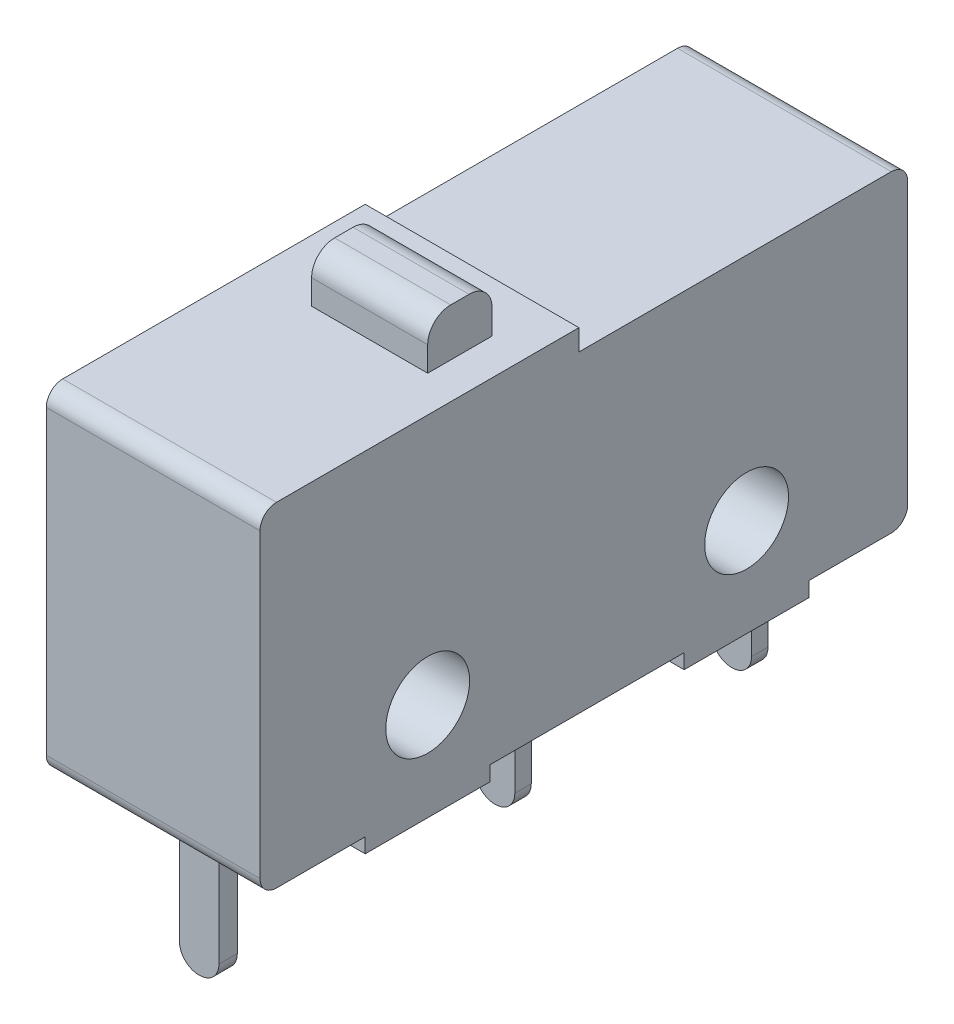
SolidWorks part; units mm, degrees
ref_plane "Front Plane" through (0, 0, 0) normal (0, 0, 1) x (1, 0, 0)
ref_plane "Top Plane" through (0, 0, 0) normal (0, 1, 0) x (1, 0, 0)
ref_plane "Right Plane" through (0, 0, 0) normal (1, 0, 0) x (0, 0, -1)
sketch "Sketch1" plane through (0, 0, 0) normal (1, 0, 0) x (0, 0, -1)
  line L0 (-37.3731, 0) -> (-34.6731, 0)
  line L1 (-37.8731, 0.5) -> (-37.8731, 9.66)
  line L2 (-37.3731, 10.16) -> (-28.1731, 10.16)
  line L3 (-28.1731, 10.16) -> (-28.1731, 9.52)
  line L4 (-28.1731, 9.52) -> (-18.6731, 9.52)
  line L5 (-18.1731, 9.02) -> (-18.1731, 0.5)
  line L6 (-34.6731, 0) -> (-34.6731, -0.45)
  line L7 (-34.6731, -0.45) -> (-30.8731, -0.45)
  line L8 (-30.8731, -0.45) -> (-30.8731, 0)
  line L9 (-30.8731, 0) -> (-24.9731, 0)
  line L10 (-24.9731, 0) -> (-24.9731, -0.45)
  line L11 (-24.9731, -0.45) -> (-21.1731, -0.45)
  line L12 (-21.1731, -0.45) -> (-21.1731, 0)
  line L13 (-21.1731, 0) -> (-18.6731, 0)
  line L14 (-32.7731, -0.45) -> (-32.7731, 2.9938) construction
  line L15 (-23.0731, -0.45) -> (-23.0731, 2.9938) construction
  arc A0 (-18.6731, 9.52) -> (-18.1731, 9.02) centre (-18.6731, 9.02) cw
  arc A1 (-18.6731, 0) -> (-18.1731, 0.5) centre (-18.6731, 0.5) ccw
  arc A2 (-37.3731, 0) -> (-37.8731, 0.5) centre (-37.3731, 0.5) cw
  arc A3 (-37.8731, 9.66) -> (-37.3731, 10.16) centre (-37.3731, 9.66) cw
  circle A4 centre (-32.7731, 2.525) radius 1.275
  circle A5 centre (-23.0731, 2.525) radius 1.275
  point P18 (-23.0731, -0.45)
  point P19 (-18.1731, 9.52)
  point P22 (-18.1731, 0)
  point P25 (-37.8731, 0)
  point P28 (-37.8731, 10.16)
  point P29 (-32.7731, -0.45)
  point P38 (-32.7731, 1.25)
  point P39 (-23.0731, 1.25)
  dimension "D11" = 0.5
  dimension "D12" = 2.55
  dimension "D13" = 2.55
  dimension "D1" = 9.52
  dimension "D2" = 10.16
  dimension "D3" = 3.8
  dimension "D4" = 3.8
  dimension "D5" = 0.45
  dimension "D6" = 0.45
  dimension "D7" = 19.7
  dimension "D8" = 3.2
  dimension "D9" = 9.7
  dimension "D10" = 5.9
  dimension "D14" = 1.7
  dimension "D15" = 1.7
extrude "Boss-Extrude1" add sketch "Sketch1" along normal blind 6.5
sketch "Sketch2" plane through (0, 10.16, 0) normal (0, 1, 0) x (1, 0, 0)
  line L0 (6.5, -28.1731) -> (6.5, -37.3731) construction
  line L1 (5.4, -31.6731) -> (1.87, -31.6731)
  line L2 (5.4, -31.6731) -> (5.4, -29.7131)
  line L3 (5.4, -29.7131) -> (1.87, -29.7131)
  line L4 (1.87, -31.6731) -> (1.87, -29.7131)
  line L5 (5.4, -31.6731) -> (1.87, -29.7131) construction
  line L6 (5.4, -29.7131) -> (1.87, -31.6731) construction
  line L7 (6.5, -37.8731) -> (0, -37.8731) construction
  point P0 (3.635, -30.6931)
  dimension "D1" = 1.96
  dimension "D2" = 3.53
  dimension "D3" = 1.1
  dimension "D4" = 6.2
extrude "Boss-Extrude2" add sketch "Sketch2" along normal blind 1.45
fillet "Fillet1" radius 0.7 2 edges at (3.635, 11.61, 29.7131) (3.635, 11.61, 31.6731)
sketch "Sketch3" plane through (0, 0, 0) normal (0, -1, 0) x (-1, 0, 0)
  line L0 (-3.25, -37.3731) -> (-3.25, -18.1731) construction
  line L1 (-6.5, -37.3731) -> (0, -37.3731) construction
  line L2 (-6.5, -18.1731) -> (0, -18.1731) construction
  line L3 (-6.5, -37.8731) -> (0, -37.8731) construction
  line L4 (-1.65, -36.4731) -> (-4.85, -36.4731)
  line L5 (-1.65, -36.4731) -> (-1.65, -35.9131)
  line L6 (-1.65, -35.9131) -> (-4.85, -35.9131)
  line L7 (-4.85, -36.4731) -> (-4.85, -35.9131)
  line L8 (-1.65, -36.4731) -> (-4.85, -35.9131) construction
  line L9 (-1.65, -35.9131) -> (-4.85, -36.4731) construction
  line L10 (-1.65, -26.9731) -> (-4.85, -26.9731)
  line L11 (-1.65, -26.9731) -> (-1.65, -27.4731)
  line L12 (-1.65, -27.4731) -> (-4.85, -27.4731)
  line L13 (-4.85, -26.9731) -> (-4.85, -27.4731)
  line L14 (-1.65, -26.9731) -> (-4.85, -27.4731) construction
  line L15 (-1.65, -27.4731) -> (-4.85, -26.9731) construction
  line L16 (-1.65, -19.7731) -> (-4.85, -19.7731)
  line L17 (-1.65, -19.7731) -> (-1.65, -20.2731)
  line L18 (-1.65, -20.2731) -> (-4.85, -20.2731)
  line L19 (-4.85, -19.7731) -> (-4.85, -20.2731)
  line L20 (-1.65, -19.7731) -> (-4.85, -20.2731) construction
  line L21 (-1.65, -20.2731) -> (-4.85, -19.7731) construction
  point P6 (-3.25, -36.1931)
  point P11 (-3.25, -27.2231)
  point P16 (-3.25, -20.0231)
  dimension "D1" = 3.2
  dimension "D2" = 0.56
  dimension "D3" = 3.2
  dimension "D4" = 0.5
  dimension "D5" = 3.2
  dimension "D6" = 0.5
  dimension "D7" = 1.6
  dimension "D8" = 1.4
  dimension "D9" = 6.7
extrude "Boss-Extrude3" add sketch "Sketch3" along normal blind 0.9
sketch "Sketch4" plane through (0, -0.9, 0) normal (0, -1, 0) x (-1, 0, 0)
  line L0 (-3.25, -36.4731) -> (-3.25, -19.7731) construction
  line L1 (-4.85, -36.4731) -> (-1.65, -36.4731) construction
  line L2 (-1.65, -19.7731) -> (-4.85, -19.7731) construction
  line L3 (-4.85, -36.4731) -> (-1.65, -36.4731) construction
  line L4 (-2.65, -36.4731) -> (-3.85, -36.4731)
  line L5 (-2.65, -36.4731) -> (-2.65, -35.9131)
  line L6 (-2.65, -35.9131) -> (-3.85, -35.9131)
  line L7 (-3.85, -36.4731) -> (-3.85, -35.9131)
  line L8 (-2.65, -36.4731) -> (-3.85, -35.9131) construction
  line L9 (-2.65, -35.9131) -> (-3.85, -36.4731) construction
  line L10 (-1.65, -35.9131) -> (-4.85, -35.9131) construction
  line L11 (-4.85, -27.4731) -> (-1.65, -27.4731) construction
  line L12 (-3.85, -26.9731) -> (-2.65, -26.9731)
  line L13 (-3.85, -26.9731) -> (-3.85, -27.4731)
  line L14 (-3.85, -27.4731) -> (-2.65, -27.4731)
  line L15 (-2.65, -26.9731) -> (-2.65, -27.4731)
  line L16 (-3.85, -26.9731) -> (-2.65, -27.4731) construction
  line L17 (-3.85, -27.4731) -> (-2.65, -26.9731) construction
  line L18 (-1.65, -26.9731) -> (-4.85, -26.9731) construction
  line L19 (-4.85, -20.2731) -> (-1.65, -20.2731) construction
  line L20 (-3.85, -19.7731) -> (-2.65, -19.7731)
  line L21 (-3.85, -19.7731) -> (-3.85, -20.2731)
  line L22 (-3.85, -20.2731) -> (-2.65, -20.2731)
  line L23 (-2.65, -19.7731) -> (-2.65, -20.2731)
  line L24 (-3.85, -19.7731) -> (-2.65, -20.2731) construction
  line L25 (-3.85, -20.2731) -> (-2.65, -19.7731) construction
  line L26 (-1.65, -19.7731) -> (-4.85, -19.7731) construction
  point P6 (-3.25, -36.1931)
  point P15 (-3.25, -27.2231)
  point P24 (-3.25, -20.0231)
  dimension "D1" = 1.2
  dimension "D2" = 1.2
  dimension "D3" = 1.2
extrude "Boss-Extrude4" add sketch "Sketch4" along normal blind 3.47
fillet "Fillet2" radius 0.59 6 edges at (2.65, -4.37, 36.1931) (3.85, -4.37, 36.1931) (2.65, -4.37, 27.2231) (3.85, -4.37, 27.2231) (3.85, -4.37, 20.0231) (2.65, -4.37, 20.0231)
